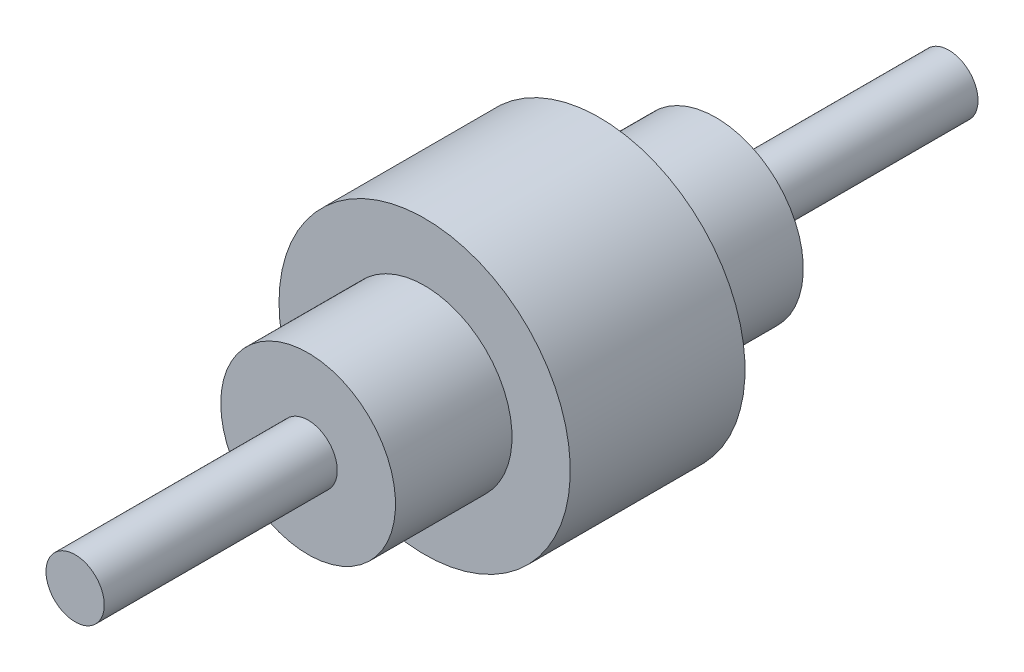
SolidWorks part; units mm, degrees
ref_plane "Alzado" through (0, 0, 0) normal (0, 0, 1) x (1, 0, 0)
ref_plane "Planta" through (0, 0, 0) normal (0, 1, 0) x (1, 0, 0)
ref_plane "Vista lateral" through (0, 0, 0) normal (1, 0, 0) x (0, 0, -1)
sketch "Croquis1" plane through (0, 0, 0) normal (1, 0, 0) x (0, 0, -1)
  line L0 (150, 0) -> (-150, 0) construction
  line L1 (-150, 0) -> (-150, 10)
  line L2 (-150, 10) -> (-70, 10)
  line L3 (-70, 10) -> (-70, 30)
  line L4 (-70, 30) -> (-30, 30)
  line L5 (-30, 30) -> (-30, 50)
  line L6 (-30, 50) -> (30, 50)
  line L7 (30, 50) -> (30, 30)
  line L8 (30, 30) -> (70, 30)
  line L9 (70, 30) -> (70, 10)
  line L10 (70, 10) -> (150, 10)
  line L11 (150, 10) -> (150, 0)
  line L12 (-150, 0) -> (150, 0)
  point P4 (0, 0)
  point P11 (0, 50)
  dimension "D1" = 20
  dimension "D2" = 80
  dimension "D3" = 60
  dimension "D4" = 40
  dimension "D5" = 100
  dimension "D6" = 300
revolve "Revolución1" add sketch "Croquis1" angle 360 about L0
equation "\"A\"= 10mm"
equation "\"D6@Croquis1\"=\"A\"*30"
equation "\"D5@Croquis1\"=\"A\"*10"
equation "\"D4@Croquis1\"=\"A\"*4"
equation "\"D2@Croquis1\"=\"A\"*8"
equation "\"D1@Croquis1\"=\"A\"*2"
equation "\"D3@Croquis1\"=\"A\"*6"
